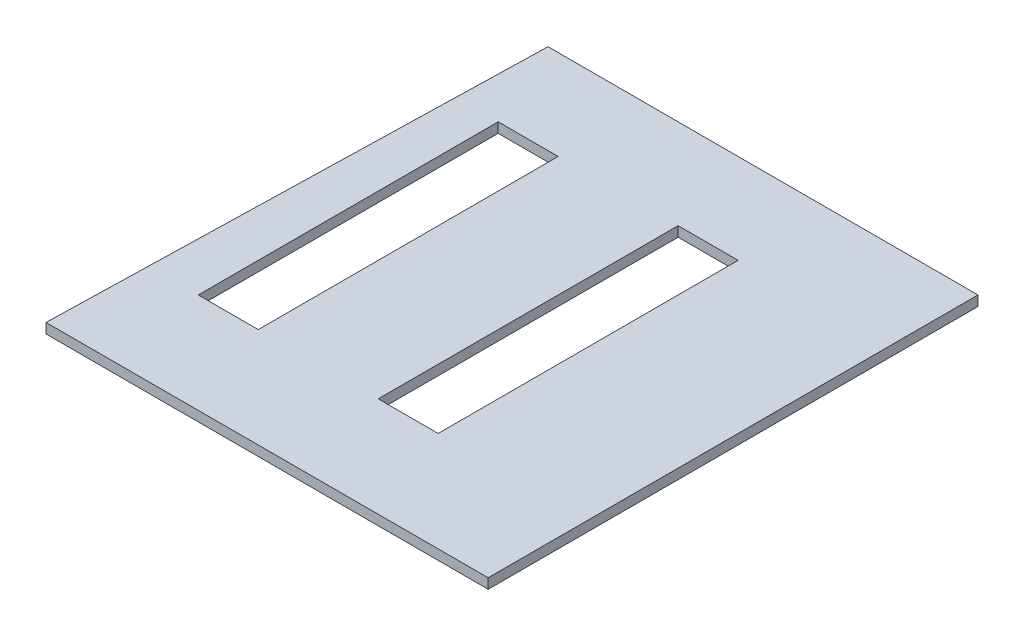
SolidWorks part; units mm, degrees
material "Polyurethane Foam Flexible"
ref_plane "Front Plane" through (0, 0, 0) normal (0, 0, 1) x (1, 0, 0)
ref_plane "Top Plane" through (0, 0, 0) normal (0, 1, 0) x (1, 0, 0)
ref_plane "Right Plane" through (0, 0, 0) normal (1, 0, 0) x (0, 0, -1)
sketch "Sketch1" plane through (0, 0, 0) normal (0, 1, 0) x (1, 0, 0)
  line L0 (-1123.8744, -1244.9382) -> (-1061.8984, 1244.2618)
  line L1 (-1061.8984, 1244.2618) -> (1123.2636, 1244.2618)
  line L3 (-1123.8744, -1244.9382) -> (1123.2636, -1244.9382)
  line L4 (1123.2636, 1244.2618) -> (1123.2636, -1244.9382)
  line L5 (-1063.5299, 1178.7339) -> (1123.2636, -1244.9382) construction
  line L6 (-1123.8744, -1244.9382) -> (1123.2636, 1244.2618) construction
  point P0 (0, 0)
  dimension "D1" = 2247.138
  dimension "D2" = 2489.2
  dimension "D3" = 2185.162
  dimension "D4" = 65.5278
extrude "Boss-Extrude1" add sketch "Sketch1" along normal blind 50.8
sketch "Sketch2" plane through (0, 50.8, 0) normal (0, 1, 0) x (1, 0, 0)
  line L0 (1123.2636, 1244.2618) -> (-1061.8984, 1244.2618) construction
  line L1 (56.4636, -736.9382) -> (361.2636, -736.9382)
  line L2 (56.4636, -736.9382) -> (56.4636, 787.0618)
  line L3 (56.4636, 787.0618) -> (361.2636, 787.0618)
  line L4 (361.2636, -736.9382) -> (361.2636, 787.0618)
  line L5 (56.4636, -736.9382) -> (361.2636, 787.0618) construction
  line L6 (56.4636, 787.0618) -> (361.2636, -736.9382) construction
  line L7 (-857.9364, -736.9382) -> (-553.1364, -736.9382)
  line L8 (-857.9364, -736.9382) -> (-857.9364, 787.0618)
  line L9 (-857.9364, 787.0618) -> (-553.1364, 787.0618)
  line L10 (-553.1364, -736.9382) -> (-553.1364, 787.0618)
  line L11 (-857.9364, -736.9382) -> (-553.1364, 787.0618) construction
  line L12 (-857.9364, 787.0618) -> (-553.1364, -736.9382) construction
  line L13 (1123.2636, -1244.9382) -> (1123.2636, 1244.2618) construction
  point P0 (208.8636, 25.0618)
  point P5 (-705.5364, 25.0618)
  dimension "D1" = 457.2
  dimension "D2" = 762
  dimension "D3" = 304.8
  dimension "D4" = 1524
  dimension "D5" = 304.8
  dimension "D6" = 609.6
extrude "Cut-Extrude1" cut sketch "Sketch2" against normal up to surface (50.8 mm away) up to face at (15.1886, 0, 0.3382)
